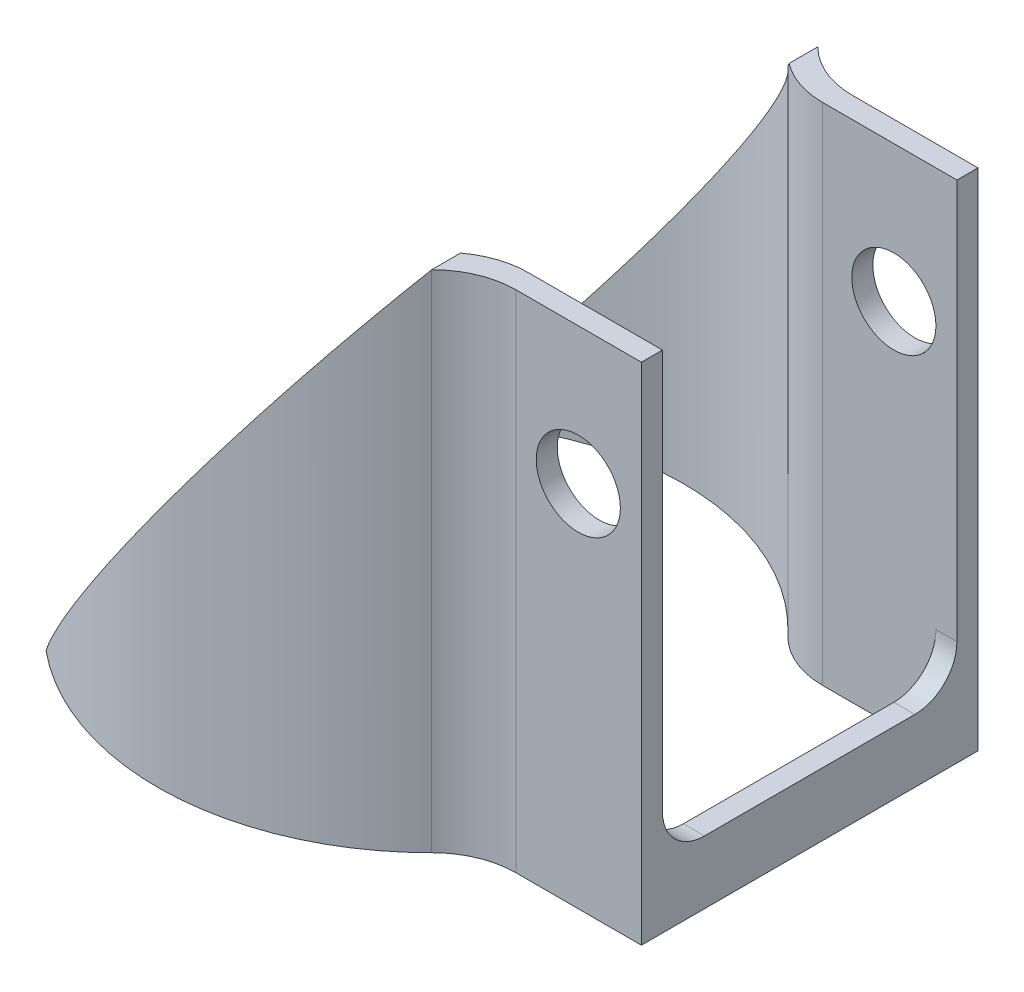
SolidWorks part; units mm, degrees
ref_plane "Front Plane" through (0, 0, 0) normal (0, 0, 1) x (1, 0, 0)
ref_plane "Top Plane" through (0, 0, 0) normal (0, 1, 0) x (1, 0, 0)
ref_plane "Right Plane" through (0, 0, 0) normal (1, 0, 0) x (0, 0, -1)
sketch "Sketch1" plane through (0, 0, 0) normal (0, 1, 0) x (1, 0, 0)
  line L0 (0, 0) -> (-33.4493, 0) construction
  line L1 (18, -8) -> (10.247, -8)
  line L2 (18, -8) -> (18, 8)
  line L3 (18, 8) -> (10.247, 8)
  line L5 (0, 0) -> (0, 25.9439) construction
  line L6 (17, -7) -> (9.7468, -7)
  line L7 (17, -7) -> (17, 7)
  line L8 (17, 7) -> (9.7468, 7)
  line L10 (17, -7) -> (3.9681, -7) construction
  line L11 (18, -8) -> (3.9681, -8) construction
  line L12 (17, 7) -> (3.9681, 7) construction
  line L13 (18, 8) -> (3.9681, 8) construction
  arc A0 (10.247, 8) -> (10.247, -8) centre (0, 0) ccw
  arc A1 (9.7468, 7) -> (9.7468, -7) centre (0, 0) ccw
  dimension "D1" = 16
  dimension "D5" = 13
  dimension "D6" = 12
  dimension "D2" = 8
  dimension "D3" = 18
  dimension "D4" = 1
extrude "Boss-Extrude1" add sketch "Sketch1" along normal blind 24
fillet "Fillet1" radius 4 4 edges at (10.247, 12, -8) (10.247, 12, 8) (9.7468, 12, -7) (9.7468, 12, 7)
ref_plane "Plane1" through (0, 0, 0) normal (0, 0, 1) x (1, 0, 0)
sketch "Sketch4" plane through (0, 0, 0) normal (0, 0, 1) x (1, 0, 0)
  line L0 (-13, 0) -> (-8.2788, 0)
  line L1 (-13, 0) -> (9.2083, 0) construction
  line L2 (-8.2788, 0) -> (9.2083, 24)
  line L3 (9.2083, 24) -> (-13, 24)
  line L4 (-13, 24) -> (-13, 0)
extrude "Cut-Extrude3" cut sketch "Sketch4" against normal through all both and the other way through all
sketch "Sketch5" plane through (0, 0, 8) normal (0, 0, 1) x (1, 0, 0)
  line L0 (12.0416, 24) -> (18, 24) construction
  line L1 (18, 24) -> (18, 0) construction
  circle A0 centre (15, 17.5) radius 2
  point P4 (15.3219, 17.5)
  dimension "D2" = 4
  dimension "D1" = 6.5
  dimension "D3" = 3
extrude "Cut-Extrude4" cut sketch "Sketch5" against normal through all both
sketch "Sketch7" plane through (18, 0, 0) normal (1, 0, 0) x (0, 0, -1)
  line L0 (0, 3.014) -> (0, -3.014) construction
  line L1 (7, 3) -> (-7, 3)
  line L4 (-7, 3) -> (-7, 25.8026)
  line L5 (-8, 0) -> (8, 0) construction
  line L6 (7, 3) -> (7, 25.8026)
  line L7 (-7, 25.8026) -> (7, 25.8026)
  dimension "D1" = 1
  dimension "D2" = 3
extrude "Cut-Extrude5" cut sketch "Sketch7" against normal through all both and the other way through all contours L7 L6 L1 L4
fillet "Fillet2" radius 2 2 edges at (17.5, 3, 7) (17.5, 3, -7)
